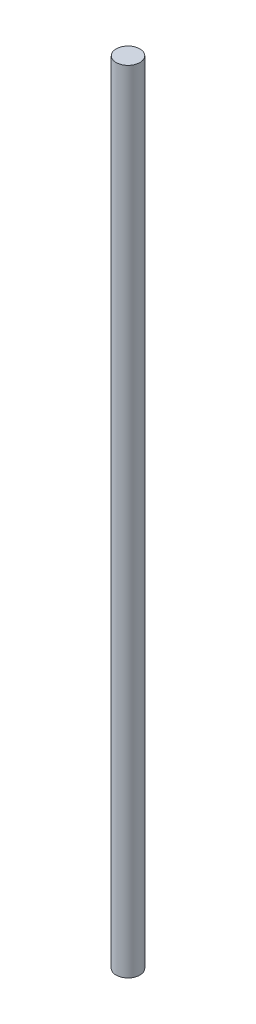
SolidWorks part; units mm, degrees
ref_plane "Front Plane" through (0, 0, 0) normal (0, 0, 1) x (1, 0, 0)
ref_plane "Top Plane" through (0, 0, 0) normal (0, 1, 0) x (1, 0, 0)
ref_plane "Right Plane" through (0, 0, 0) normal (1, 0, 0) x (0, 0, -1)
sketch "Sketch1" plane through (0, 0, 0) normal (0, 1, 0) x (1, 0, 0)
  circle A0 centre (0, 0) radius 6
extrude "Boss-Extrude1" add sketch "Sketch1" along normal blind 400
